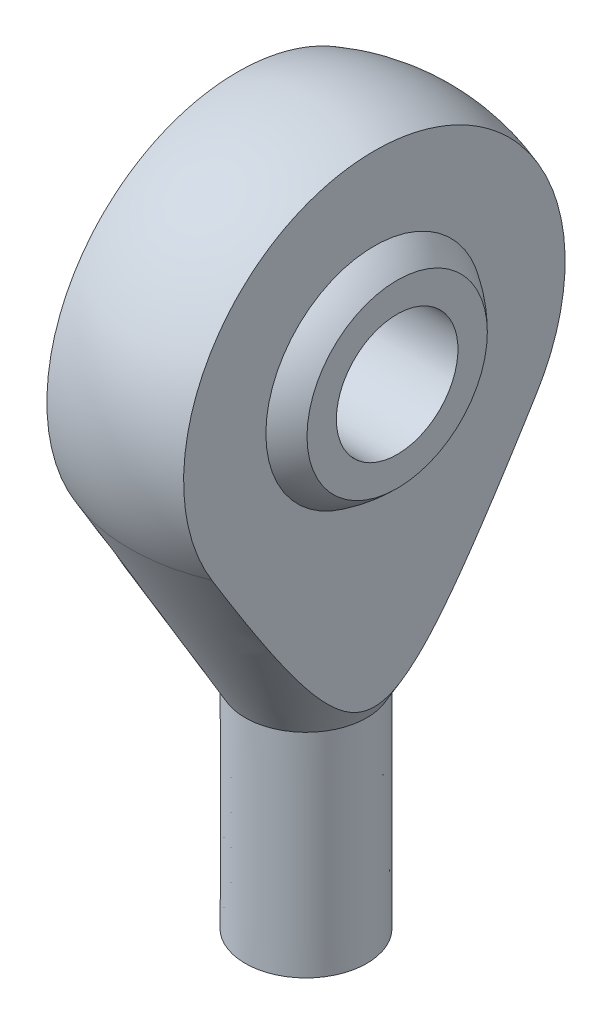
SolidWorks part; units mm, degrees
ref_plane "Płaszczyzna XY" through (0, 0, 0) normal (0, 0, 1) x (1, 0, 0)
ref_plane "Płaszczyzna XZ" through (0, 0, 0) normal (0, 1, 0) x (1, 0, 0)
ref_plane "Płaszczyzna YZ" through (0, 0, 0) normal (1, 0, 0) x (0, 0, -1)
sketch "Szkic1" plane through (0, 0, 0) normal (0, 0, 1) x (1, 0, 0)
  line L0 (-3, 0) -> (3, 0)
  line L1 (3, 0) -> (3, 21)
  line L2 (3, 21) -> (-3, 21) construction
  line L3 (-3, 21) -> (-3, 0)
  line L4 (-3, 21) -> (-8.6992, 31.0772)
  line L5 (3, 21) -> (8.7057, 31.0704)
  line L6 (0.0052, 46) -> (0, 0)
  arc A0 (8.7057, 31.0704) -> (-8.6992, 31.0772) centre (0.0052, 36) ccw
  point P4 (0, 0)
  dimension "D2" = 20
  dimension "D1" = 6
  dimension "D3" = 36
  dimension "GL" = 21
revolve "Obrót4" add sketch "Szkic1" angle 360 about L6
sketch "Szkic2" plane through (0, 0, 0) normal (0, 0, 1) x (1, 0, 0)
  line L0 (-20, 46) -> (20, 46)
  line L1 (20, 46) -> (20, 10.8573)
  line L2 (20, 10.8573) -> (3.375, 21.6537)
  line L3 (3.375, 21.6537) -> (3.375, 46)
  line L4 (-20, 46) -> (-20, 10.8667)
  line L5 (-20, 10.8667) -> (-3.375, 21.6631)
  line L6 (-3.375, 21.6631) -> (-3.375, 46)
  line L7 (0, 35.7786) -> (0, -51.7786) construction
  line L8 (-8.6992, 31.0772) -> (-3, 21) construction
  line L9 (3.0047, 20.9993) -> (8.7062, 31.0753) construction
  point P9 (0, 46)
  point P12 (0, -8)
  dimension "M" = 6.75
  dimension "D1" = 3.375
  dimension "D2" = 40
  dimension "D3" = 54
  dimension "D4" = 123
  dimension "D5" = 123
extrude "Wytnij-wyciągnięcie1" cut sketch "Szkic2" against normal through all both and the other way through all contours L5 L6 L0 L4 | L3 L2 L1 L0
sketch "Szkic3" plane through (0, 0, 0) normal (1, 0, 0) x (0, 0, -1)
  line L3 (0, 0) -> (0, 10.5388) construction
ref_plane "Płaszczyzna1" through (0, 0, 0) normal (0, 0, -1) x (0, 1, 0)
sketch "Szkic4" plane through (0, 0, 0) normal (0, 0, -1) x (0, 1, 0)
  line L0 (-200000, 0) -> (200010.5388, 0) construction
  line L1 (35.9993, -1) -> (35.9993, 16.5523) construction
  line L2 (31.5493, -4.5) -> (40.4493, -4.5)
  line L3 (31.5493, -4.5) -> (31.5493, 4.5)
  line L4 (31.5493, 4.5) -> (40.4493, 4.5)
  line L5 (40.4493, -4.5) -> (40.4493, 4.5)
  line L6 (31.5493, -4.5) -> (40.4493, 4.5) construction
  line L7 (31.5493, 4.5) -> (40.4493, -4.5) construction
  line L8 (32.9993, -4.5) -> (38.9993, -4.5)
  line L9 (32.9993, -4.5) -> (32.9993, 4.5)
  line L10 (32.9993, 4.5) -> (38.9993, 4.5)
  line L11 (38.9993, -4.5) -> (38.9993, 4.5)
  line L12 (32.9993, -4.5) -> (38.9993, 4.5) construction
  line L13 (32.9993, 4.5) -> (38.9993, -4.5) construction
  circle A0 centre (35.9993, 0) radius 6.3287
  dimension "D1" = 6
  dimension "D2" = 8.9
  dimension "D3" = 9
  dimension "D4" = 36
revolve "Obrót5" add sketch "Szkic4" angle 360 about L1
sketch "Szkic8" plane through (0, 0, 0) normal (1, 0, 0) x (0, 0, -1)
  circle A0 centre (0, 35.9993) radius 3
extrude "Wytnij-wyciągnięcie3" cut sketch "Szkic8" against normal through all both and the other way through all
sketch "Szkic9" [suppressed] plane through (0, 0, 0) normal (1, 0, 0) x (0, 0, -1)
  circle A0 centre (0, 41.9991) radius 4
extrude "Wytnij-wyciągnięcie4" [suppressed] cut sketch "Szkic9" against normal through all both and the other way through all
ref_point "Point1" [suppressed]
sketch "Sketch2" plane through (0, 0, 0) normal (1, 0, 0) x (0, 0, -1)
  line L10 (-8.625, -1.8186) -> (10.3296, -1.8186)
  line L11 (-8.625, -1.8186) -> (-8.625, 10.4997)
  line L12 (-8.625, 10.4997) -> (10.3296, 10.4997)
  line L13 (10.3296, -1.8186) -> (10.3296, 10.4997)
  line L14 (-2.9998, -1.8186) -> (-0.7841, -1.8186)
extrude "Cut-Extrude2" cut sketch "Sketch2" against normal through all both and the other way through all contours L10 L13 L12 L11
equation "\"D2@Szkic2\"=2*\"D2@Szkic1\""
equation "\"D1@Szkic2\"=\"M@Szkic2\"/2mm"
